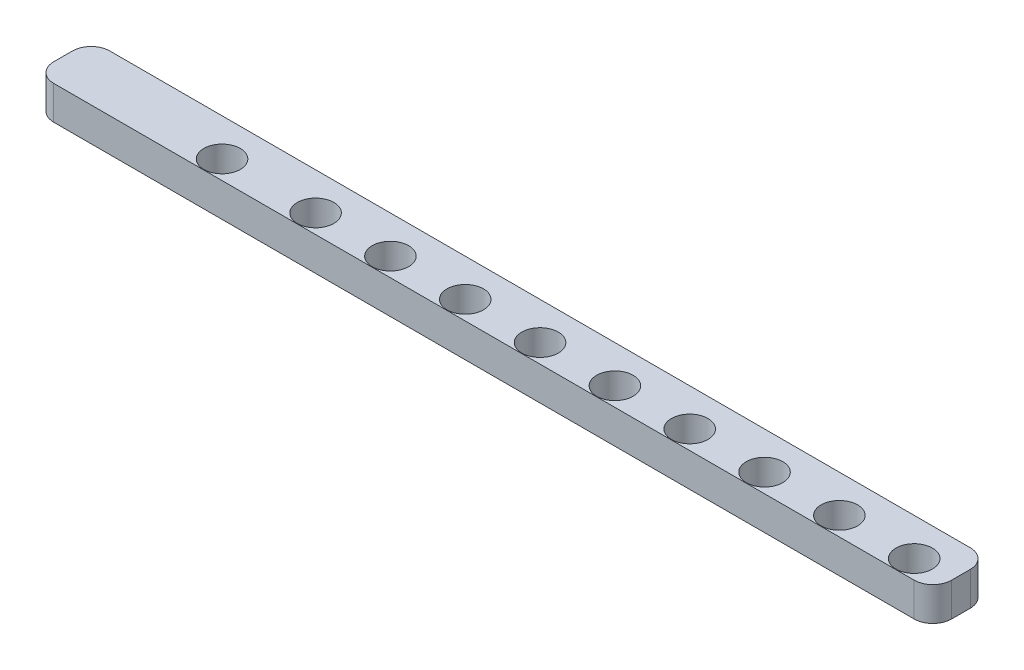
SolidWorks part; units mm, degrees
ref_plane "Front Plane" through (0, 0, 0) normal (0, 0, 1) x (1, 0, 0)
ref_plane "Top Plane" through (0, 0, 0) normal (0, 1, 0) x (1, 0, 0)
ref_plane "Right Plane" through (0, 0, 0) normal (1, 0, 0) x (0, 0, -1)
sketch "Sketch1" plane through (0, 0, 0) normal (0, 1, 0) x (1, 0, 0)
  line L1 (2, 0) -> (94, 0)
  line L2 (0, -2) -> (0, -4)
  line L3 (2, -6) -> (94, -6)
  line L4 (96, -2) -> (96, -4)
  arc A0 (94, -6) -> (96, -4) centre (94, -4) ccw
  arc A1 (0, -4) -> (2, -6) centre (2, -4) ccw
  arc A2 (2, 0) -> (0, -2) centre (2, -2) ccw
  arc A3 (94, 0) -> (96, -2) centre (94, -2) cw
  point P7 (96, -6)
  point P12 (0, 0)
  point P15 (96, 0)
  dimension "D3" = 2
  dimension "D1" = 96
  dimension "D2" = 6
extrude "Boss-Extrude1" add sketch "Sketch1" along normal blind 3.6
sketch "Sketch2" plane through (0, 3.6, 0) normal (0, 1, 0) x (1, 0, 0)
  line L0 (94, 0) -> (2, 0) construction
  line L1 (96, -4) -> (96, -2) construction
  line L2 (92, -4) -> (0, -4) construction
  line L3 (0, -2) -> (0, -4) construction
  circle A0 centre (92, -4) radius 1.95
  circle A1 centre (84, -4) radius 1.95
  circle A2 centre (18, -4) radius 1.95
  circle A3 centre (28, -4) radius 1.95
  circle A4 centre (36, -4) radius 1.95
  circle A5 centre (44, -4) radius 1.95
  circle A6 centre (52, -4) radius 1.95
  circle A7 centre (60, -4) radius 1.95
  circle A8 centre (68, -4) radius 1.95
  circle A9 centre (76, -4) radius 1.95
  dimension "D1" = 3.9
  dimension "D4" = 3.9
  dimension "D7" = 3.9
  dimension "D8" = 3.9
  dimension "D9" = 3.9
  dimension "D10" = 3.9
  dimension "D11" = 3.9
  dimension "D12" = 3.9
  dimension "D13" = 3.9
  dimension "D14" = 3.9
  dimension "D2" = 4
  dimension "D3" = 4
  dimension "D5" = 8
  dimension "D6" = 18
  dimension "D15" = 8
  dimension "D16" = 8
  dimension "D17" = 8
  dimension "D18" = 8
  dimension "D19" = 8
  dimension "D20" = 8
  dimension "D21" = 8
extrude "Cut-Extrude1" cut sketch "Sketch2" against normal blind 3.6
